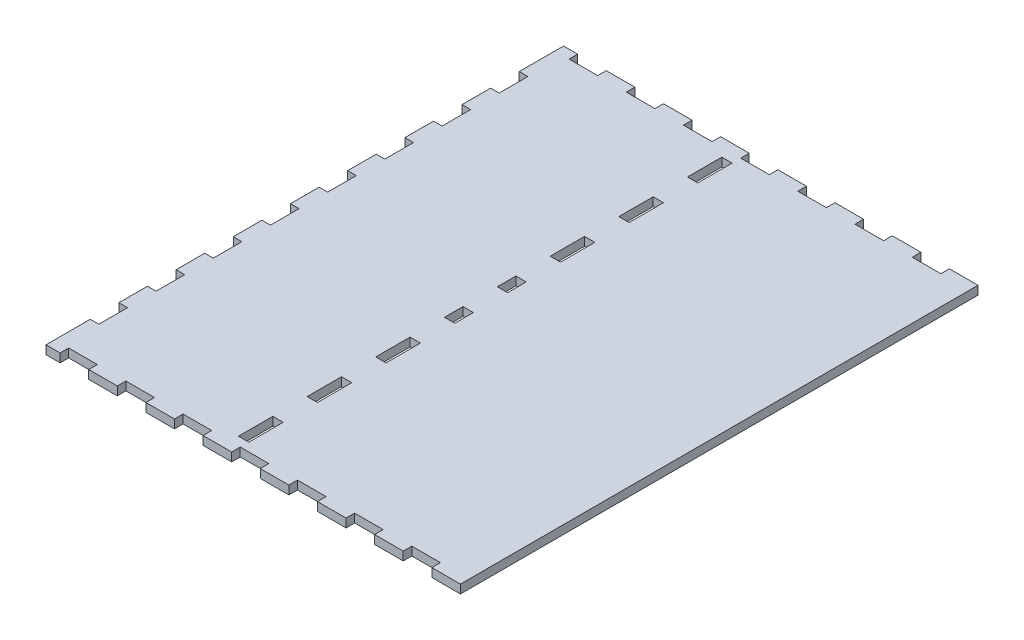
SolidWorks part; units mm, degrees
ref_plane "Front Plane" through (0, 0, 0) normal (0, 0, 1) x (1, 0, 0)
ref_plane "Top Plane" through (0, 0, 0) normal (0, 1, 0) x (1, 0, 0)
ref_plane "Right Plane" through (0, 0, 0) normal (1, 0, 0) x (0, 0, -1)
sketch "Sketch1" plane through (0, 0, 0) normal (0, 1, 0) x (1, 0, 0)
  line L0 (0, 90.5) -> (144.93, 90.5) construction
  line L2 (0, 0) -> (0, 15.5)
  line L3 (0, 181) -> (4.93, 181)
  line L4 (144.93, 0) -> (144.93, 181)
  line L5 (72.465, 181) -> (72.465, 0) construction
  line L6 (134.93, 181) -> (134.93, 178)
  line L7 (134.93, 178) -> (124.93, 178)
  line L8 (124.93, 178) -> (124.93, 181)
  line L9 (134.93, 178) -> (144.93, 178) construction
  line L10 (104.93, 178) -> (104.93, 181)
  line L11 (114.93, 178) -> (104.93, 178)
  line L12 (114.93, 181) -> (114.93, 178)
  line L13 (84.93, 178) -> (84.93, 181)
  line L14 (94.93, 178) -> (84.93, 178)
  line L15 (94.93, 181) -> (94.93, 178)
  line L16 (64.93, 178) -> (64.93, 181)
  line L17 (74.93, 178) -> (64.93, 178)
  line L18 (74.93, 181) -> (74.93, 178)
  line L19 (44.93, 178) -> (44.93, 181)
  line L20 (54.93, 178) -> (44.93, 178)
  line L21 (54.93, 181) -> (54.93, 178)
  line L22 (24.93, 178) -> (24.93, 181)
  line L23 (34.93, 178) -> (24.93, 178)
  line L24 (34.93, 181) -> (34.93, 178)
  line L25 (4.93, 178) -> (4.93, 181)
  line L26 (14.93, 178) -> (4.93, 178)
  line L27 (14.93, 181) -> (14.93, 178)
  line L28 (14.93, 181) -> (24.93, 181)
  line L29 (34.93, 181) -> (44.93, 181)
  line L30 (54.93, 181) -> (64.93, 181)
  line L31 (74.93, 181) -> (84.93, 181)
  line L32 (94.93, 181) -> (104.93, 181)
  line L33 (114.93, 181) -> (124.93, 181)
  line L34 (134.93, 181) -> (144.93, 181)
  line L35 (134.93, 3) -> (144.93, 3) construction
  line L36 (134.93, 0) -> (144.93, 0)
  line L37 (114.93, 0) -> (124.93, 0)
  line L38 (94.93, 0) -> (104.93, 0)
  line L39 (74.93, 0) -> (84.93, 0)
  line L40 (54.93, 0) -> (64.93, 0)
  line L41 (34.93, 0) -> (44.93, 0)
  line L42 (14.93, 0) -> (24.93, 0)
  line L43 (14.93, 0) -> (14.93, 3)
  line L44 (14.93, 3) -> (4.93, 3)
  line L45 (4.93, 3) -> (4.93, 0)
  line L46 (34.93, 0) -> (34.93, 3)
  line L47 (34.93, 3) -> (24.93, 3)
  line L48 (24.93, 3) -> (24.93, 0)
  line L49 (54.93, 0) -> (54.93, 3)
  line L50 (54.93, 3) -> (44.93, 3)
  line L51 (44.93, 3) -> (44.93, 0)
  line L52 (74.93, 0) -> (74.93, 3)
  line L53 (74.93, 3) -> (64.93, 3)
  line L54 (64.93, 3) -> (64.93, 0)
  line L55 (94.93, 0) -> (94.93, 3)
  line L56 (94.93, 3) -> (84.93, 3)
  line L57 (84.93, 3) -> (84.93, 0)
  line L58 (114.93, 0) -> (114.93, 3)
  line L59 (114.93, 3) -> (104.93, 3)
  line L60 (104.93, 3) -> (104.93, 0)
  line L61 (124.93, 3) -> (124.93, 0)
  line L62 (134.93, 3) -> (124.93, 3)
  line L63 (134.93, 0) -> (134.93, 3)
  line L64 (0, 0) -> (4.93, 0)
  line L65 (0, 15.5) -> (3, 15.5)
  line L66 (3, 15.5) -> (3, 25.5)
  line L67 (3, 25.5) -> (0, 25.5)
  line L68 (3, 15.5) -> (3, 0) construction
  line L69 (0, 25.5) -> (0, 35.5)
  line L70 (3, 45.5) -> (0, 45.5)
  line L71 (3, 35.5) -> (3, 45.5)
  line L72 (0, 35.5) -> (3, 35.5)
  line L73 (3, 65.5) -> (0, 65.5)
  line L74 (3, 55.5) -> (3, 65.5)
  line L75 (0, 55.5) -> (3, 55.5)
  line L76 (3, 85.5) -> (0, 85.5)
  line L77 (3, 75.5) -> (3, 85.5)
  line L78 (0, 75.5) -> (3, 75.5)
  line L79 (3, 105.5) -> (0, 105.5)
  line L80 (3, 95.5) -> (3, 105.5)
  line L81 (0, 95.5) -> (3, 95.5)
  line L82 (3, 125.5) -> (0, 125.5)
  line L83 (3, 115.5) -> (3, 125.5)
  line L84 (0, 115.5) -> (3, 115.5)
  line L85 (3, 145.5) -> (0, 145.5)
  line L86 (3, 135.5) -> (3, 145.5)
  line L87 (0, 135.5) -> (3, 135.5)
  line L88 (3, 165.5) -> (0, 165.5)
  line L89 (3, 155.5) -> (3, 165.5)
  line L90 (0, 155.5) -> (3, 155.5)
  line L91 (0, 165.5) -> (0, 181)
  line L92 (0, 145.5) -> (0, 155.5)
  line L93 (0, 125.5) -> (0, 135.5)
  line L94 (0, 105.5) -> (0, 115.5)
  line L95 (0, 45.5) -> (0, 55.5)
  line L96 (0, 65.5) -> (0, 75.5)
  line L97 (0, 85.5) -> (0, 95.5)
  dimension "D1" = 181
  dimension "D2" = 144.93
  dimension "D3" = 10
  dimension "D4" = 10
  dimension "D5" = 3
  dimension "D7" = 15.5
  dimension "D8" = 10
  dimension "D9" = 3
  dimension "D6" = 7
  dimension "D10" = 8
extrude "Boss-Extrude1" add sketch "Sketch1" along normal blind 3
sketch "Sketch2" plane through (0, 0, 0) normal (0, -1, 0) x (1, 0, 0)
  line L0 (61.33, -30) -> (61.33, -42) construction
  line L1 (61.33, -42) -> (64.93, -42) construction
  line L2 (64.93, -42) -> (64.93, -30) construction
  line L3 (64.93, -30) -> (61.33, -30) construction
  line L4 (61.33, -6) -> (61.33, -18) construction
  line L5 (61.33, -18) -> (64.93, -18) construction
  line L6 (64.93, -18) -> (64.93, -6) construction
  line L7 (64.93, -6) -> (61.33, -6) construction
  line L8 (61.33, -30) -> (61.33, -42)
  line L9 (61.33, -42) -> (64.93, -42)
  line L10 (64.93, -42) -> (64.93, -30)
  line L11 (64.93, -30) -> (61.33, -30)
  line L12 (61.33, -6) -> (61.33, -18)
  line L13 (61.33, -18) -> (64.93, -18)
  line L14 (64.93, -18) -> (64.93, -6)
  line L15 (64.93, -6) -> (61.33, -6)
  line L16 (61.33, -163) -> (61.33, -175) construction
  line L17 (61.33, -175) -> (64.93, -175) construction
  line L18 (64.93, -175) -> (64.93, -163) construction
  line L19 (64.93, -163) -> (61.33, -163) construction
  line L20 (61.33, -139) -> (61.33, -151) construction
  line L21 (61.33, -151) -> (64.93, -151) construction
  line L22 (64.93, -151) -> (64.93, -139) construction
  line L23 (64.93, -139) -> (61.33, -139) construction
  line L24 (61.33, -115) -> (61.33, -127) construction
  line L25 (61.33, -127) -> (64.93, -127) construction
  line L26 (64.93, -127) -> (64.93, -115) construction
  line L27 (64.93, -115) -> (61.33, -115) construction
  line L28 (61.33, -96.5) -> (61.33, -103) construction
  line L29 (61.33, -103) -> (64.93, -103) construction
  line L30 (64.93, -103) -> (64.93, -96.5) construction
  line L31 (64.93, -96.5) -> (61.33, -96.5) construction
  line L32 (61.33, -78) -> (61.33, -84.5) construction
  line L33 (61.33, -84.5) -> (64.93, -84.5) construction
  line L34 (64.93, -84.5) -> (64.93, -78) construction
  line L35 (64.93, -78) -> (61.33, -78) construction
  line L36 (61.33, -54) -> (61.33, -66) construction
  line L37 (61.33, -66) -> (64.93, -66) construction
  line L38 (64.93, -66) -> (64.93, -54) construction
  line L39 (64.93, -54) -> (61.33, -54) construction
  line L40 (61.33, -163) -> (61.33, -175)
  line L41 (61.33, -175) -> (64.93, -175)
  line L42 (64.93, -175) -> (64.93, -163)
  line L43 (64.93, -163) -> (61.33, -163)
  line L44 (61.33, -139) -> (61.33, -151)
  line L45 (61.33, -151) -> (64.93, -151)
  line L46 (64.93, -151) -> (64.93, -139)
  line L47 (64.93, -139) -> (61.33, -139)
  line L48 (61.33, -115) -> (61.33, -127)
  line L49 (61.33, -127) -> (64.93, -127)
  line L50 (64.93, -127) -> (64.93, -115)
  line L51 (64.93, -115) -> (61.33, -115)
  line L52 (61.33, -96.5) -> (61.33, -103)
  line L53 (61.33, -103) -> (64.93, -103)
  line L54 (64.93, -103) -> (64.93, -96.5)
  line L55 (64.93, -96.5) -> (61.33, -96.5)
  line L56 (61.33, -78) -> (61.33, -84.5)
  line L57 (61.33, -84.5) -> (64.93, -84.5)
  line L58 (64.93, -84.5) -> (64.93, -78)
  line L59 (64.93, -78) -> (61.33, -78)
  line L60 (61.33, -54) -> (61.33, -66)
  line L61 (61.33, -66) -> (64.93, -66)
  line L62 (64.93, -66) -> (64.93, -54)
  line L63 (64.93, -54) -> (61.33, -54)
extrude "Cut-Extrude1" cut sketch "Sketch2" against normal blind 10
